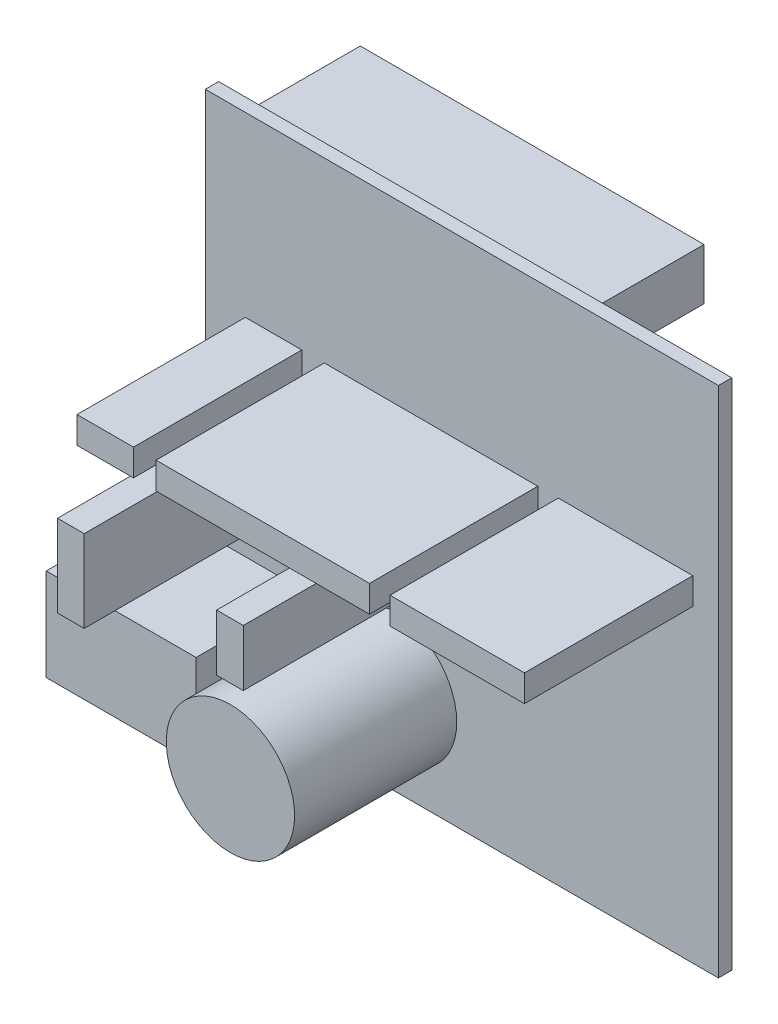
SolidWorks part; units mm, degrees
ref_plane "Alzado" through (0, 0, 0) normal (0, 0, 1) x (1, 0, 0)
ref_plane "Planta" through (0, 0, 0) normal (0, 1, 0) x (1, 0, 0)
ref_plane "Vista lateral" through (0, 0, 0) normal (1, 0, 0) x (0, 0, -1)
sketch "Croquis1" plane through (0, 0, 0) normal (0, 0, 1) x (1, 0, 0)
  line L1 (0, 0) -> (50, 0)
  line L2 (0, 0) -> (0, -50)
  line L3 (0, -50) -> (50, -50)
  line L4 (50, 0) -> (50, -50)
  dimension "D1" = 50
  dimension "D2" = 50
extrude "Saliente-Extruir1" add sketch "Croquis1" along normal blind 1.3
sketch "Croquis2" plane through (0, 0, 0) normal (0, 0, -1) x (-1, 0, 0)
  line L0 (-50, 0) -> (0, 0) construction
  line L1 (-2.7, -1.2) -> (-36.2, -1.2)
  line L2 (-2.7, -1.2) -> (-2.7, -6.2)
  line L3 (-2.7, -6.2) -> (-36.2, -6.2)
  line L4 (-36.2, -1.2) -> (-36.2, -6.2)
  line L5 (0, 0) -> (0, -50) construction
  dimension "D1" = 33.5
  dimension "D2" = 5
  dimension "D3" = 1.2
  dimension "D4" = 2.7
extrude "Saliente-Extruir2" add sketch "Croquis2" along normal blind 11.1
sketch "Croquis3" plane through (0, 0, 1.3) normal (0, 0, 1) x (1, 0, 0)
  line L0 (0, 0) -> (0, -50) construction
  line L1 (-4.6, -46.5) -> (10, -46.5)
  line L2 (-4.6, -46.5) -> (-4.6, -37.5)
  line L3 (-4.6, -37.5) -> (10, -37.5)
  line L4 (10, -46.5) -> (10, -37.5)
  line L5 (0, -50) -> (50, -50) construction
  dimension "D1" = 14.6
  dimension "D2" = 9
  dimension "D3" = 4.6
  dimension "D4" = 3.5
extrude "Saliente-Extruir3" add sketch "Croquis3" along normal blind 10.9
sketch "Croquis4" plane through (0, 0, 1.3) normal (0, 0, 1) x (1, 0, 0)
  line L0 (0, -50) -> (50, -50) construction
  line L1 (10, -46.5) -> (10, -37.5) construction
  circle A0 centre (18.25, -41.15) radius 6.25
  point P2 (18.25, -47.4)
  point P5 (12, -41.15)
  dimension "D1" = 12.5
  dimension "D2" = 2.6
  dimension "D3" = 2
extrude "Saliente-Extruir4" add sketch "Croquis4" along normal blind 15.8
sketch "Croquis5" plane through (0, 0, 1.3) normal (0, 0, 1) x (1, 0, 0)
  line L0 (50, -17.3) -> (0, -17.3) construction
  line L1 (50, -50) -> (50, 0) construction
  line L2 (0, 0) -> (0, -37.5) construction
  line L3 (50, 0) -> (0, 0) construction
  line L4 (47.5, -17.3) -> (34.4, -17.3)
  line L5 (47.5, -17.3) -> (47.5, -19.9)
  line L6 (47.5, -19.9) -> (34.4, -19.9)
  line L7 (34.4, -17.3) -> (34.4, -19.9)
  line L8 (32.4, -17.3) -> (11.6, -17.3)
  line L9 (32.4, -17.3) -> (32.4, -19.9)
  line L10 (32.4, -19.9) -> (11.6, -19.9)
  line L11 (11.6, -17.3) -> (11.6, -19.9)
  line L12 (9.4, -17.3) -> (3.9, -17.3)
  line L13 (9.4, -17.3) -> (9.4, -19.9)
  line L14 (9.4, -19.9) -> (3.9, -19.9)
  line L15 (3.9, -17.3) -> (3.9, -19.9)
  line L16 (0, -27) -> (50, -27) construction
  line L18 (2, -27) -> (4.6, -27)
  line L19 (2, -27) -> (2, -35)
  line L20 (2, -35) -> (4.6, -35)
  line L21 (4.6, -27) -> (4.6, -35)
  line L22 (17.5, -27) -> (20.1, -27)
  line L23 (17.5, -27) -> (17.5, -32.5)
  line L24 (17.5, -32.5) -> (20.1, -32.5)
  line L25 (20.1, -27) -> (20.1, -32.5)
  dimension "D1" = 17.3
  dimension "D2" = 2.5
  dimension "D3" = 2.6
  dimension "D4" = 13.1
  dimension "D5" = 2
  dimension "D6" = 20.8
  dimension "D7" = 2.2
  dimension "D8" = 5.5
  dimension "D9" = 8
  dimension "D10" = 5.5
  dimension "D11" = 27
  dimension "D12" = 2
  dimension "D13" = 12.9
extrude "Saliente-Extruir5" add sketch "Croquis5" along normal blind 16.4
